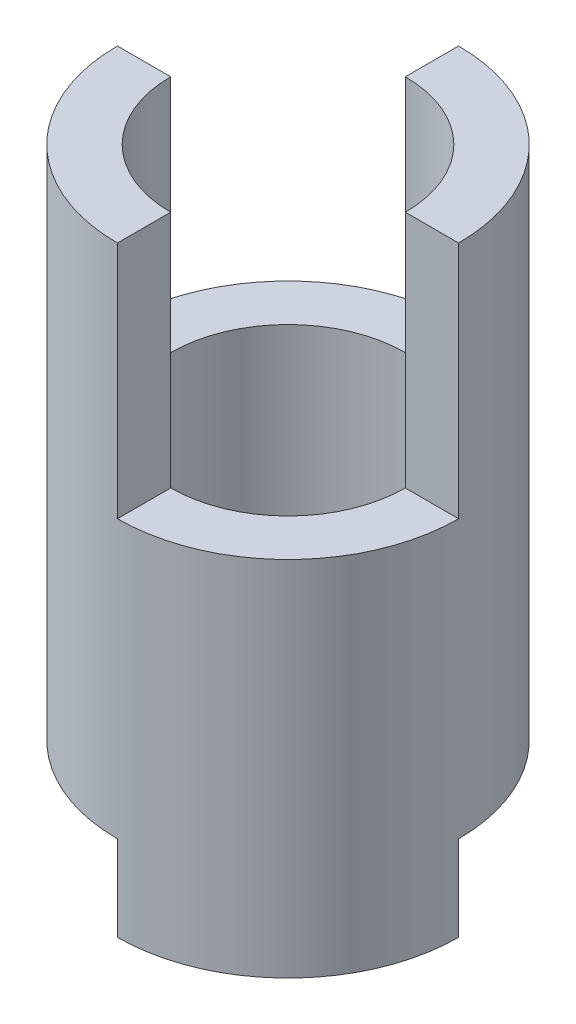
SolidWorks part; units mm, degrees
material "Acrilico (impatto medio-alto)"
ref_plane "Piano frontale" through (0, 0, 0) normal (0, 0, 1) x (1, 0, 0)
ref_plane "Piano superiore" through (0, 0, 0) normal (0, 1, 0) x (1, 0, 0)
ref_plane "Piano destro" through (0, 0, 0) normal (1, 0, 0) x (0, 0, -1)
sketch "Schizzo1" plane through (0, 0, 0) normal (0, 1, 0) x (1, 0, 0)
  circle A0 centre (0, 0) radius 4
  circle A1 centre (0, 0) radius 2.75
  dimension "D1" = 8
  dimension "D2" = 5.5
extrude "Estrusione-Estrusione2" add sketch "Schizzo1" along normal blind 14.1 contours A0 | A1
sketch "Schizzo2" plane through (0, 14.1, 0) normal (0, 1, 0) x (1, 0, 0)
  line L0 (0, 2.75) -> (0, 4)
  line L1 (2.75, 0) -> (4, 0)
  line L2 (-2.75, 0) -> (-4, 0)
  line L3 (0, -2.75) -> (0, -4)
  arc A0 (0, -4) -> (4, 0) centre (0, 0) ccw
  arc A1 (0, -2.75) -> (2.75, 0) centre (0, 0) ccw
  arc A2 (0, 2.75) -> (-2.75, 0) centre (0, 0) ccw
  arc A3 (0, 4) -> (-4, 0) centre (0, 0) ccw
extrude "Taglio-Estrusione1" cut sketch "Schizzo2" against normal blind 5.6
sketch "Schizzo3" plane through (0, 0, 0) normal (0, -1, 0) x (1, 0, 0)
  line L0 (0, 2.75) -> (0, 4)
  line L1 (2.75, 0) -> (4, 0)
  line L2 (-2.75, 0) -> (-4, 0)
  line L3 (0, -2.75) -> (0, -4)
  arc A0 (0, -2.75) -> (2.75, 0) centre (0, 0) ccw
  arc A1 (0, -4) -> (4, 0) centre (0, 0) ccw
  arc A2 (0, 2.75) -> (-2.75, 0) centre (0, 0) ccw
  arc A3 (0, 4) -> (-4, 0) centre (0, 0) ccw
extrude "Taglio-Estrusione2" cut sketch "Schizzo3" against normal blind 2
equation "\"3.5.00mm\"=7"
